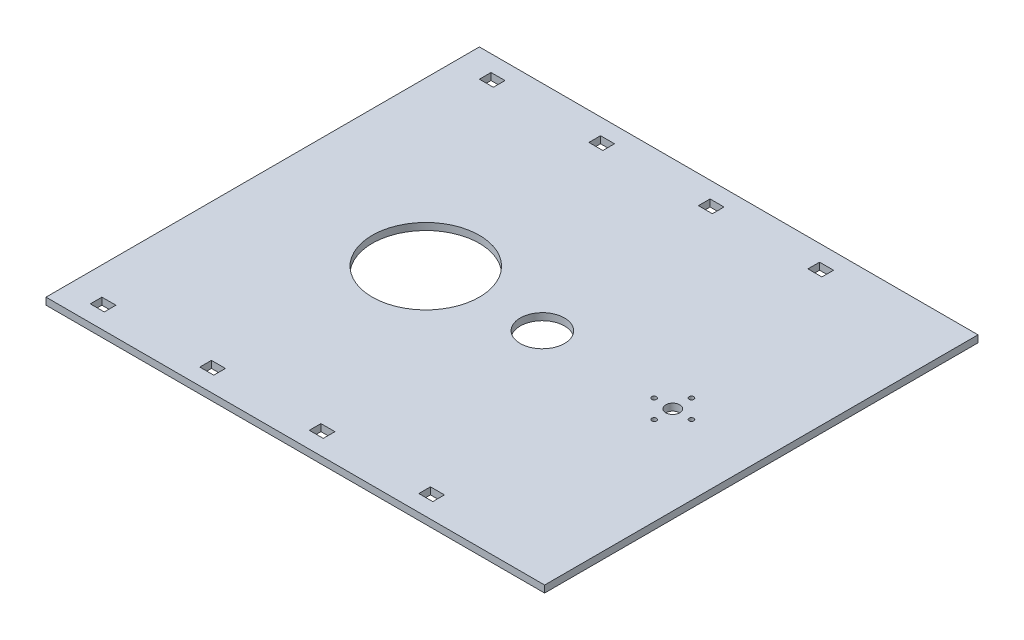
SolidWorks part; units mm, degrees
ref_plane "Front Plane" through (0, 0, 0) normal (0, 0, 1) x (1, 0, 0)
ref_plane "Top Plane" through (0, 0, 0) normal (0, 1, 0) x (1, 0, 0)
ref_plane "Right Plane" through (0, 0, 0) normal (1, 0, 0) x (0, 0, -1)
sketch "Sketch1" plane through (0, 0, 0) normal (0, 1, 0) x (1, 0, 0)
  line L1 (-112.5896, 53.8993) -> (101.4104, 53.8993)
  line L2 (-112.5896, 53.8993) -> (-112.5896, -132.1007)
  line L3 (-112.5896, -132.1007) -> (101.4104, -132.1007)
  line L4 (101.4104, 53.8993) -> (101.4104, -132.1007)
  dimension "D1" = 214
  dimension "D2" = 186
extrude "Boss-Extrude1" add sketch "Sketch1" along normal blind 3
sketch "Sketch2" plane through (0, 3, 0) normal (0, 1, 0) x (1, 0, 0)
  line L0 (-112.5896, 53.8993) -> (-112.5896, -132.1007) construction
  line L1 (-112.5896, -39.1007) -> (-99.6901, -39.1007) construction
  circle A0 centre (-42.5896, -39.1007) radius 23
  dimension "D2" = 46
  dimension "D1" = 70
extrude "Speaker" cut sketch "Sketch2" against normal through all
sketch "Sketch4" plane through (0, 3, 0) normal (0, 1, 0) x (1, 0, 0)
  line L0 (101.4104, -132.1007) -> (101.4104, 53.8993) construction
  line L1 (63.4104, -39.1007) -> (59.3917, -39.1007) construction
  line L2 (101.4104, -39.1007) -> (94.8057, -39.1007) construction
  circle A0 centre (63.4104, -39.1007) radius 3
  circle B0 centre (63.4104, -39.1007) radius 10.7 construction
  circle B1 centre (63.4104, -31.1007) radius 1.025
  circle B2 centre (71.4104, -39.1007) radius 1.025
  circle B3 centre (63.4104, -47.1007) radius 1.025
  circle B4 centre (55.4104, -39.1007) radius 1.025
  dimension "D2" = 6
  dimension "D1" = 30
sketch_block_instance "Block2-1"
sketch_block "Block2"
extrude "Motor" cut sketch "Sketch4" against normal through all
sketch "Sketch6" plane through (0, 3, 0) normal (0, 1, 0) x (1, 0, 0)
  line L0 (-112.5896, -39.1007) -> (-93.2571, -39.1007) construction
  line L1 (-94.5896, -125.1007) -> (-53.5896, -125.1007) construction
  line L2 (-47.5896, -125.1007) -> (-6.5896, -125.1007) construction
  line L5 (-100.5896, -125.1007) -> (-94.5896, -125.1007)
  line L6 (-100.5896, -125.1007) -> (-100.5896, -120.1007)
  line L7 (-100.5896, -120.1007) -> (-94.5896, -120.1007)
  line L8 (-94.5896, -125.1007) -> (-94.5896, -120.1007)
  line L9 (-53.5896, -125.1007) -> (-47.5896, -125.1007)
  line L10 (-53.5896, -125.1007) -> (-53.5896, -120.1007)
  line L11 (-53.5896, -120.1007) -> (-47.5896, -120.1007)
  line L12 (-47.5896, -125.1007) -> (-47.5896, -120.1007)
  line L13 (-6.5896, -125.1007) -> (-0.5896, -125.1007)
  line L14 (-6.5896, -125.1007) -> (-6.5896, -120.1007)
  line L15 (-6.5896, -120.1007) -> (-0.5896, -120.1007)
  line L16 (-0.5896, -125.1007) -> (-0.5896, -120.1007)
  line L17 (-94.5896, 46.8993) -> (-53.5896, 46.8993) construction
  line L18 (-47.5896, 46.8993) -> (-6.5896, 46.8993) construction
  line L19 (-100.5896, 46.8993) -> (-94.5896, 46.8993)
  line L20 (-100.5896, 46.8993) -> (-100.5896, 41.8993)
  line L21 (-100.5896, 41.8993) -> (-94.5896, 41.8993)
  line L22 (-94.5896, 46.8993) -> (-94.5896, 41.8993)
  line L23 (-53.5896, 46.8993) -> (-47.5896, 46.8993)
  line L24 (-53.5896, 46.8993) -> (-53.5896, 41.8993)
  line L25 (-53.5896, 41.8993) -> (-47.5896, 41.8993)
  line L26 (-47.5896, 46.8993) -> (-47.5896, 41.8993)
  line L27 (-6.5896, 46.8993) -> (-0.5896, 46.8993)
  line L28 (-6.5896, 46.8993) -> (-6.5896, 41.8993)
  line L29 (-6.5896, 41.8993) -> (-0.5896, 41.8993)
  line L30 (-0.5896, 46.8993) -> (-0.5896, 41.8993)
  line L31 (46.4104, -125.1007) -> (46.4104, -120.1007)
  line L32 (40.4104, 46.8993) -> (46.4104, 46.8993)
  line L33 (40.4104, 46.8993) -> (40.4104, 41.8993)
  line L34 (40.4104, 41.8993) -> (46.4104, 41.8993)
  line L35 (46.4104, 46.8993) -> (46.4104, 41.8993)
  line L36 (40.4104, -120.1007) -> (46.4104, -120.1007)
  line L37 (40.4104, -125.1007) -> (40.4104, -120.1007)
  line L38 (40.4104, -125.1007) -> (46.4104, -125.1007)
  dimension "D2" = 6
  dimension "D3" = 6
  dimension "D4" = 41
  dimension "D5" = 6
  dimension "D6" = 41
  dimension "D7" = 6
  dimension "D8" = 5
  dimension "D9" = 5
  dimension "D10" = 5
  dimension "D11" = 6
  dimension "D12" = 41
  dimension "D13" = 6
  dimension "D14" = 41
  dimension "D15" = 6
  dimension "D16" = 5
  dimension "D17" = 5
  dimension "D18" = 5
  dimension "D19" = 41
extrude "Izgaralar" cut sketch "Sketch6" against normal through all
sketch "Sketch7" plane through (0, 3, 0) normal (0, 1, 0) x (1, 0, 0)
  line L0 (101.4104, -132.1007) -> (101.4104, 53.8993) construction
  circle A0 centre (6.4104, -38.0656) radius 9.5
  dimension "D1" = 19
  dimension "D2" = 95
extrude "Motor Kablosu" cut sketch "Sketch7" against normal through all
